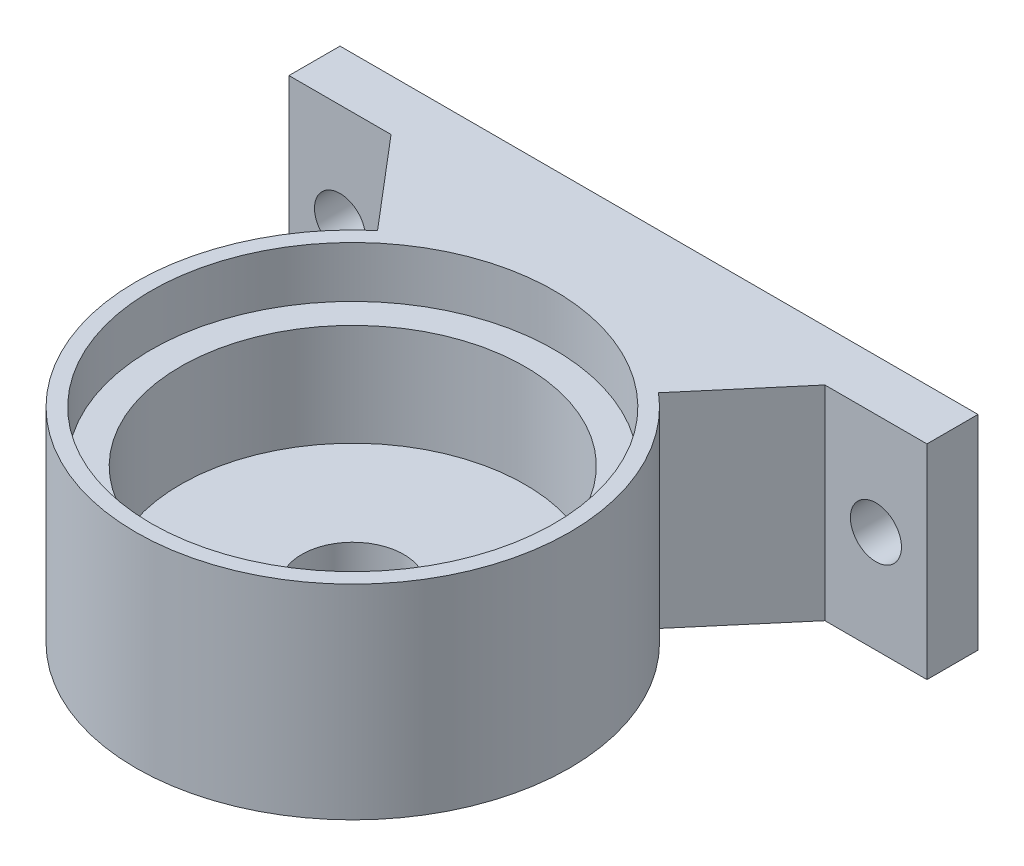
SolidWorks part; units mm, degrees
ref_plane "前视基准面" through (0, 0, 0) normal (0, 0, 1) x (1, 0, 0)
ref_plane "上视基准面" through (0, 0, 0) normal (0, 1, 0) x (1, 0, 0)
ref_plane "右视基准面" through (0, 0, 0) normal (1, 0, 0) x (0, 0, -1)
sketch "草图1" plane through (0, 0, 0) normal (0, 1, 0) x (1, 0, 0)
  circle A0 centre (0, 0) radius 6.75
  circle A1 centre (0, 0) radius 8
  dimension "D1" = 13.5
  dimension "D2" = 16
extrude "凸台-拉伸2" add sketch "草图1" along normal blind 6
sketch "草图2" plane through (0, 0, 0) normal (0, 1, 0) x (1, 0, 0)
  circle A0 centre (0, 0) radius 6.75
  circle A1 centre (0, 0) radius 2
  dimension "D1" = 4
extrude "凸台-拉伸3" add sketch "草图2" along normal blind 2
sketch "草图3" plane through (0, 6, 0) normal (0, 1, 0) x (1, 0, 0)
  circle A0 centre (0, 0) radius 7.9
  circle A1 centre (0, 0) radius 8.5
  dimension "D1" = 15.8
  dimension "D2" = 17
extrude "凸台-拉伸4" add sketch "草图3" along normal blind 2
sketch "草图4" plane through (0, 6, 0) normal (0, -1, 0) x (1, 0, 0)
  circle A0 centre (0, 0) radius 8
  circle A1 centre (0, 0) radius 8.5
extrude "凸台-拉伸6" add sketch "草图4" along normal blind 6
sketch "草图6" plane through (0, 0, 0) normal (0, -1, 0) x (1, 0, 0)
  line L0 (-8.5, -10) -> (-5.505, -6.4765)
  line L1 (0, -12) -> (12.5, -12)
  line L2 (0, -12) -> (-12.5, -12)
  line L3 (-12.5, -12) -> (-12.5, -10)
  line L4 (5.505, -6.4765) -> (8.5, -10)
  line L5 (12.5, -10) -> (12.5, -12)
  line L6 (-12.5, -10) -> (-8.5, -10)
  line L7 (8.5, -10) -> (12.5, -10)
  circle A6 centre (0, 0) radius 8.5 construction
  arc A7 (5.505, -6.4765) -> (-5.505, -6.4765) centre (0, 0) cw
  dimension "D1" = 12.5
  dimension "D2" = 12.5
  dimension "D3" = 2
extrude "凸台-拉伸8" add sketch "草图6" against normal blind 8
sketch "草图7" plane through (0, 0, -12) normal (0, 0, -1) x (-1, 0, 0)
  circle A0 centre (10.5, 4) radius 1
  circle A1 centre (-10.5, 4) radius 1
  dimension "D3" = 2
  dimension "D4" = 2
extrude "切除-拉伸1" cut sketch "草图7" against normal blind 8
